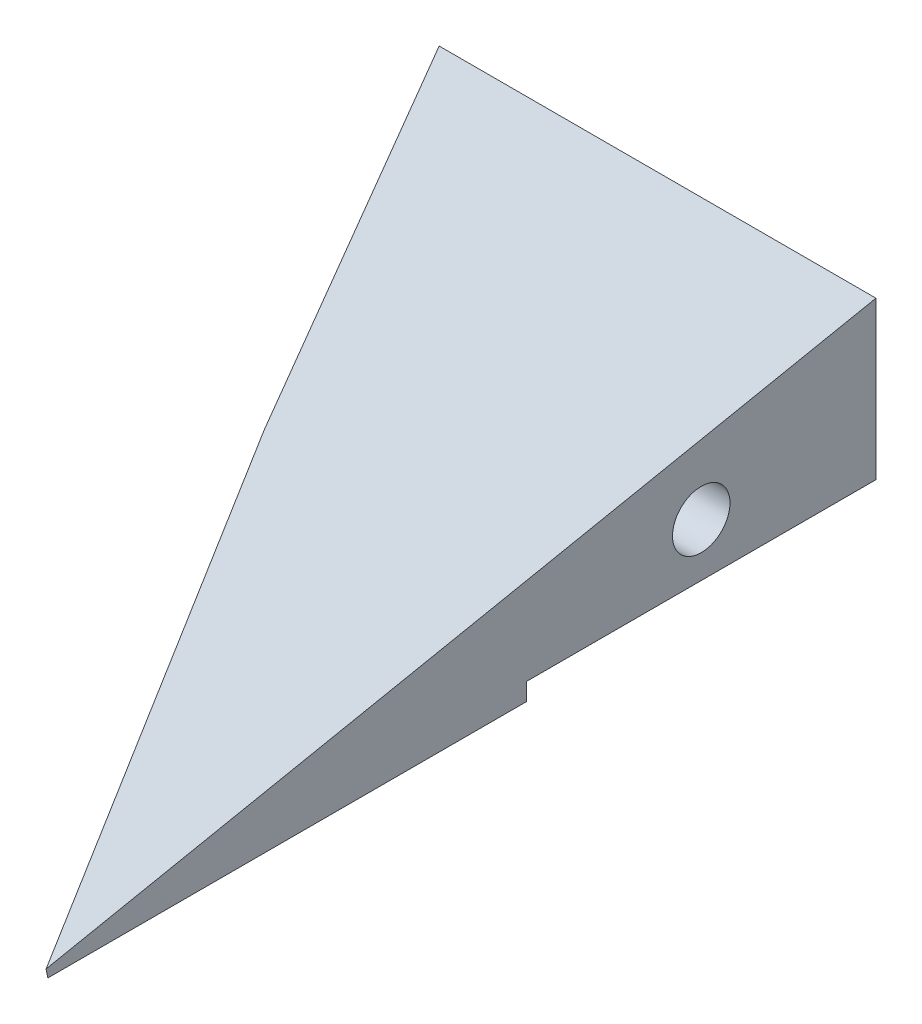
SolidWorks part; units mm, degrees
material "AISI 1020"
ref_plane "Plano frontal" through (0, 0, 0) normal (0, 0, 1) x (1, 0, 0)
ref_plane "Plano superior" through (0, 0, 0) normal (0, 1, 0) x (1, 0, 0)
ref_plane "Plano direito" through (0, 0, 0) normal (1, 0, 0) x (0, 0, -1)
sketch "Esboço1" plane through (0, 0, 0) normal (0, 0, 1) x (1, 0, 0)
  line L1 (-65, 10) -> (65, 10)
  line L2 (-65, 10) -> (-65, -10)
  line L3 (-65, -10) -> (65, -10)
  line L4 (65, 10) -> (65, -10)
  line L5 (-65, 10) -> (65, -10) construction
  line L6 (-65, -10) -> (65, 10) construction
  point P0 (0, 0)
  dimension "D1" = 130
  dimension "D2" = 20
extrude "Ressalto-extrusão1" add sketch "Esboço1" along normal blind 95
sketch "Esboço2" plane through (0, 10, 0) normal (0, 1, 0) x (1, 0, 0)
  line L0 (15, 0) -> (-65, 0)
  line L2 (65, -95) -> (65, 0) construction
  line L3 (35, -40) -> (15, 0)
  line L4 (-65, -95) -> (-65, 0) construction
  line L6 (-65, -95) -> (-65, 0)
  line L7 (65, -95) -> (-65, -95) construction
  line L8 (65, 0) -> (-65, 0) construction
  line L9 (5, -95) -> (-65, -95)
  line L10 (35, -40) -> (35, -41)
  line L11 (35, -41) -> (5, -41)
  line L12 (5, -41) -> (5, -95)
  dimension "D3" = 70
  dimension "D5" = 1
  dimension "D1" = 50
  dimension "D2" = 30
  dimension "D4" = 40
extrude "Corte-extrusão2" cut sketch "Esboço2" against normal up to next contours L3 L0 L6 L9 L12 L11 L10
sketch "Esboço3" plane through (65, 0, 0) normal (1, 0, 0) x (0, 0, -1)
  line L0 (0, 10) -> (-95, -9)
  line L1 (-95, -10) -> (-95, 10) construction
  dimension "D1" = 1
extrude "Corte-extrusão3" cut sketch "Esboço3" against normal through all and the other way through all flip side to cut
hole_wizard "Broca de rosquear de cano para tarraxa de 1/82" positions "Esboço7" profile "Esboço8" hole size "1/8" standard "Ansi Inch"
sketch "Esboço7" plane through (65, 0, 0) normal (1, 0, 0) x (0, 0, -1)
  line L0 (0, -10) -> (0, 10) construction
  line L1 (-95, -10) -> (0, -10) construction
  point P0 (-20, -1.945)
  dimension "D1" = 20
  dimension "D2" = 8.055
sketch "Esboço8" plane through (65, -1.945, 20) normal (0, 1, 0) x (0, 0, -1)
  line L0 (0, 0) -> (0, 11.9768)
  line L1 (0, 11.9768) -> (3.29, 10)
  line L2 (3.29, 10) -> (3.29, 0)
  line L5 (3.29, 0) -> (0, 0)
  line L10 (0, 11.9768) -> (-3.29, 10) construction
  line L11 (0, -6.35) -> (0, 107.95) construction
  dimension "Hole Dia." = 6.58
  dimension "Hole Depth" = 10
  dimension "Drill Angle" = 118
hole_wizard "Broca de rosquear de cano para tarraxa de 1/83" positions "Esboço10" profile "Esboço11" hole size "1/8" standard "Ansi Inch"
sketch "Esboço10" plane through (12, 0, -6) normal (-0.8944, 0, 0.4472) x (0.4472, 0, 0.8944)
  line L0 (6.7082, -10) -> (6.7082, 10) construction
  line L1 (6.7082, -10) -> (51.4296, -10) construction
  point P0 (26.7082, -1.945)
  dimension "D1" = 20
  dimension "D2" = 8.055
sketch "Esboço11" plane through (23.9443, -1.945, 17.8885) normal (0, 1, 0) x (0.4472, 0, 0.8944)
  line L0 (0, 0) -> (0, 11.9768)
  line L1 (0, 11.9768) -> (3.29, 10)
  line L2 (3.29, 10) -> (3.29, 0)
  line L5 (3.29, 0) -> (0, 0)
  line L10 (0, 11.9768) -> (-3.29, 10) construction
  line L11 (0, -6.35) -> (0, 107.95) construction
  dimension "Hole Dia." = 6.58
  dimension "Hole Depth" = 10
  dimension "Drill Angle" = 118
sketch "Esboço12" plane through (0, 0, 0) normal (0, 0, -1) x (-1, 0, 0)
  line L0 (-15, -10) -> (-15, 10) construction
  line L1 (-65, -10) -> (-15, -10)
  line L2 (-65, -10) -> (-65, -8)
  line L3 (-65, -8) -> (-15, -8)
  line L4 (-15, -10) -> (-15, -8)
  dimension "D1" = 2
extrude "Corte-extrusão4" cut sketch "Esboço12" against normal blind 40
sketch "Esboço13" plane through (0, 9.6154, 1.9231) normal (0, 0.9806, 0.1961) x (1, 0, 0)
  line L0 (35, -38.831) -> (65, -94.9202)
  line L1 (65, -94.9202) -> (66.5585, -100.0963)
  line L2 (66.5585, -100.0963) -> (-6.3795, -94.9202)
  line L3 (-6.3795, -94.9202) -> (-1.8208, -30.681)
  line L5 (35, -38.831) -> (34.2695, -39.5615)
  line L6 (34.2695, -39.5615) -> (-1.8208, -30.681)
extrude "Corte-extrusão5" cut sketch "Esboço13" against normal through all
